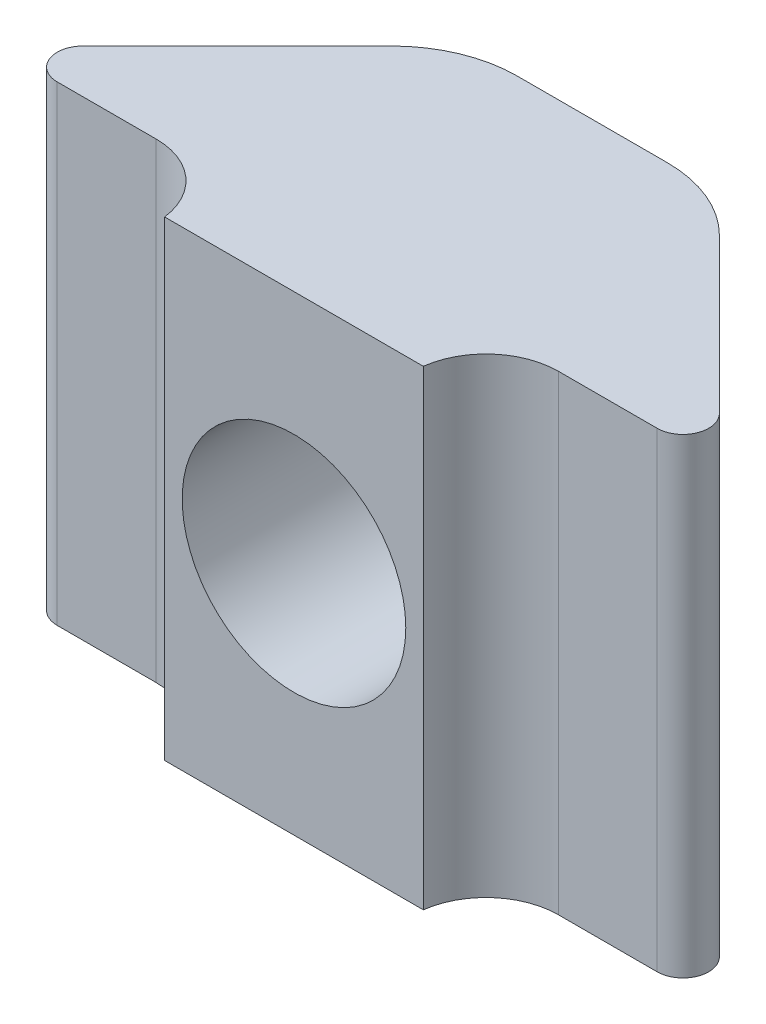
SolidWorks part; units mm, degrees
ref_plane "Front Plane" through (0, 0, 0) normal (0, 0, 1) x (1, 0, 0)
ref_plane "Top Plane" through (0, 0, 0) normal (0, 1, 0) x (1, 0, 0)
ref_plane "Right Plane" through (0, 0, 0) normal (1, 0, 0) x (0, 0, -1)
sketch "Sketch1" plane through (0, 0, 0) normal (0, 1, 0) x (1, 0, 0)
  line L11 (-4.3434, -5.2744) -> (-6.4748, -5.2744)
  line L12 (-2.7913, -6.6393) -> (2.7913, -6.6393)
  line L19 (6.4748, -5.2744) -> (4.3434, -5.2744)
  line L20 (3.5379, -0.9952) -> (6.8679, -4.3252)
  line L21 (-1.6181, -0.2) -> (1.6181, -0.2)
  line L22 (-6.8679, -4.3252) -> (-3.5379, -0.9952)
  arc A12 (-6.8679, -4.3252) -> (-6.4748, -5.2744) centre (-6.4748, -4.7184) ccw
  arc A13 (-2.7913, -6.6393) -> (-4.3434, -5.2744) centre (-4.3434, -6.8393) ccw
  arc A14 (4.3434, -5.2744) -> (2.7913, -6.6393) centre (4.3434, -6.8393) ccw
  arc A15 (6.4748, -5.2744) -> (6.8679, -4.3252) centre (6.4748, -4.7184) ccw
  arc A16 (3.5379, -0.9952) -> (1.6181, -0.2) centre (1.6181, -2.915) ccw
  arc A17 (-1.6181, -0.2) -> (-3.5379, -0.9952) centre (-1.6181, -2.915) ccw
extrude "Boss-Extrude1" add sketch "Sketch1" along normal blind 10.16
sketch "Sketch2" plane through (0, 0, 6.6393) normal (0, 0, 1) x (1, 0, 0)
  line L0 (-2.7913, 0) -> (2.7913, 10.16) construction
  circle A0 centre (0, 5.08) radius 2.413
  dimension "D1" = 4.826
extrude "Cut-Extrude1" cut sketch "Sketch2" against normal through all contours A0
